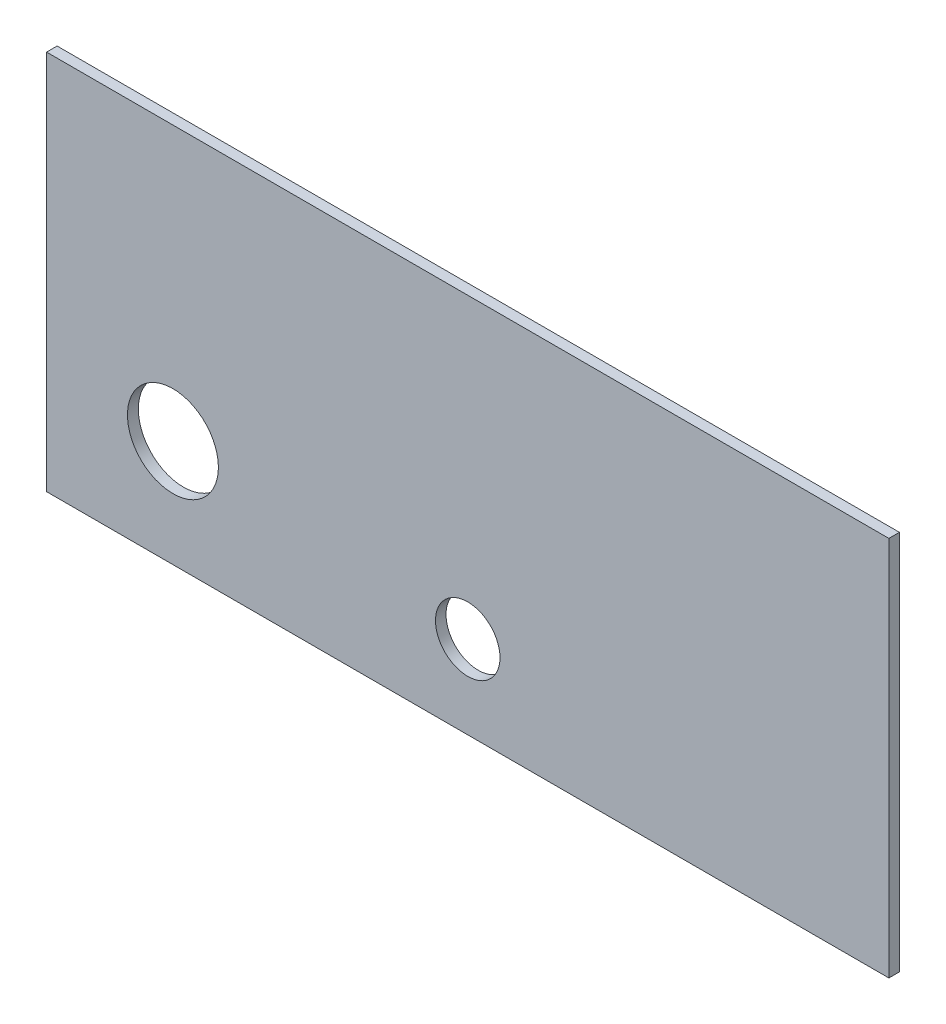
SolidWorks part; units mm, degrees
material "Acrylic (Medium-high impact)"
ref_plane "Front Plane" through (0, 0, 0) normal (0, 0, 1) x (1, 0, 0)
ref_plane "Top Plane" through (0, 0, 0) normal (0, 1, 0) x (1, 0, 0)
ref_plane "Right Plane" through (0, 0, 0) normal (1, 0, 0) x (0, 0, -1)
sketch "Sketch2" plane through (0, 0, 0) normal (0, 0, 1) x (1, 0, 0)
  line L0 (63.5, 12.5001) -> (63.5, 0) construction
  line L5 (0, 0) -> (127, 0)
  line L6 (0, 0) -> (0, 57.404)
  line L7 (0, 57.404) -> (127, 57.404)
  line L8 (127, 0) -> (127, 57.404)
  circle A0 centre (63.5, 12.5001) radius 4.864
  circle A2 centre (63.5, 12.5001) radius 4.864 construction
  dimension "D5" = 12.5001
  dimension "D6" = 9.728
  dimension "D1" = 0
  dimension "D2" = 0
  dimension "D3" = 127
  dimension "D4" = 57.404
extrude "Boss-Extrude1" add sketch "Sketch2" against normal blind 1.5875
hole_wizard "1/4 NPT Tapped Hole1" positions "Sketch4" profile "Sketch3" size "1/4" standard "ANSI Inch" end condition through all
sketch "Sketch4" plane through (0, 0, 0) normal (0, 0, 1) x (1, 0, 0)
  line L0 (0, 57.404) -> (0, 0) construction
  line L1 (127, 57.404) -> (0, 57.404) construction
  point P0 (19.05, 16.129)
  dimension "D1" = 19.05
  dimension "D2" = 41.275
sketch "Sketch3" plane through (19.05, 16.129, 0) normal (1, 0, 0) x (0, -1, 0)
  line L0 (0, 0) -> (0, 1.5875)
  line L1 (0, 1.5875) -> (5.5626, 1.5875)
  line L2 (-6.558, 9.906) -> (-6.8546, 0) construction
  line L3 (5.5626, 1.5875) -> (5.5626, 9.906)
  line L4 (5.5626, 9.906) -> (6.558, 9.906)
  line L5 (6.558, 9.906) -> (6.8546, 0)
  line L7 (6.8546, 0) -> (0, 0)
  line L8 (0, -6.35) -> (0, 107.95) construction
  line L11 (-5.5626, 9.906) -> (-6.558, 9.906) construction
  dimension "Thru Tap Drill Dia." = 11.1252
  dimension "Thru Tap Drill Depth" = 1.5875
  dimension "Thread Dia." = 13.7092
  dimension "Thread Angle" = 3.43
  dimension "Thread Depth" = 9.906
